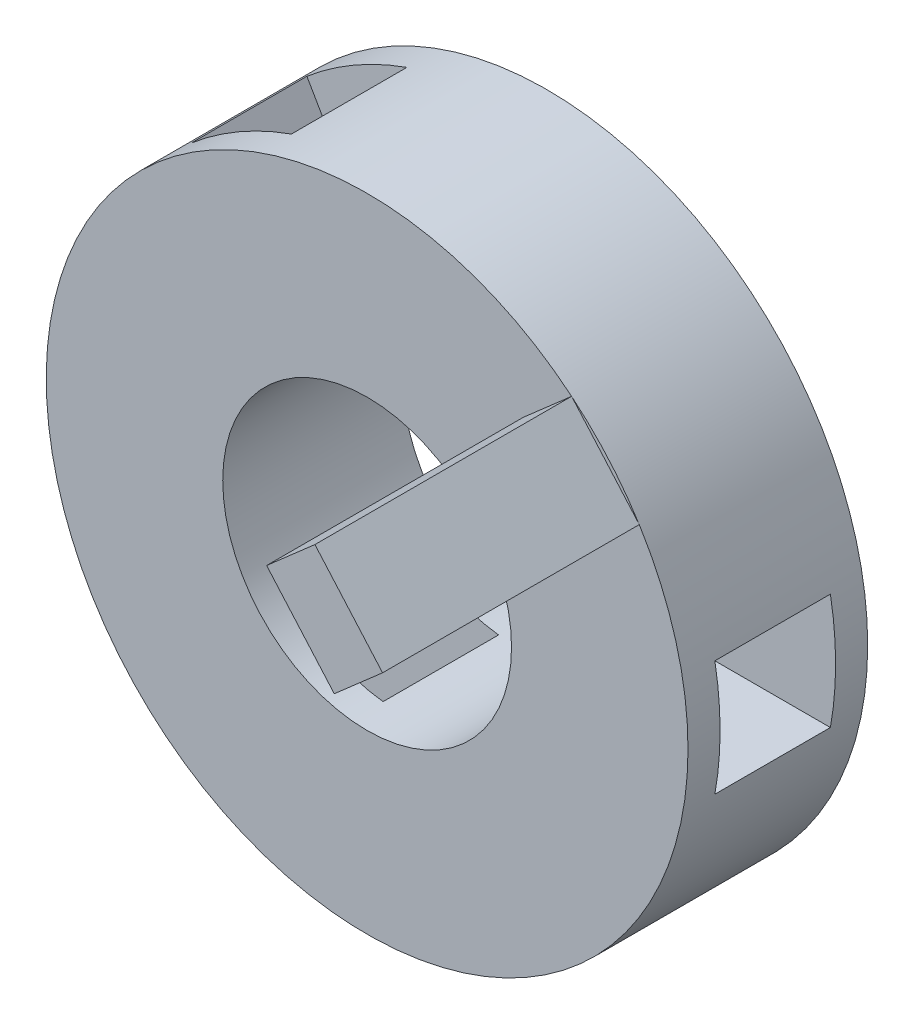
SolidWorks part; units mm, degrees
ref_plane "Plan de face" through (0, 0, 0) normal (0, 0, 1) x (1, 0, 0)
ref_plane "Plan de dessus" through (0, 0, 0) normal (0, 1, 0) x (1, 0, 0)
ref_plane "Plan de droite" through (0, 0, 0) normal (1, 0, 0) x (0, 0, -1)
sketch "Esquisse1" plane through (0, 0, 0) normal (0, 0, 1) x (1, 0, 0)
  circle A0 centre (0, 0) radius 25
  dimension "D1" = 50
extrude "Boss.-Extru.1" add sketch "Esquisse1" along normal blind 14 contours A0
sketch "Esquisse2" plane through (0, 0, 0) normal (1, 0, 0) x (0, 0, -1)
  line L0 (0, -25) -> (0, 25) construction
  line L1 (-11.5, 4.5) -> (-2.5, 4.5)
  line L2 (-11.5, 4.5) -> (-11.5, -4.5)
  line L3 (-11.5, -4.5) -> (-2.5, -4.5)
  line L4 (-2.5, 4.5) -> (-2.5, -4.5)
  dimension "D1" = 9
  dimension "D2" = 9
  dimension "D3" = 2.5
  dimension "D5" = 4.5
extrude "Enlèv. mat.-Extru.1" cut sketch "Esquisse2" against normal blind 16 from offset 26
pattern_circular "Répétition circulaire1" count 3 over 360 about axis through (0, 0, 0) along (0, 0, 1) of "Enlèv. mat.-Extru.1"
sketch "Esquisse9" plane through (0, 0, 0) normal (0, 0, -1) x (-1, 0, 0)
  circle A0 centre (0, 0) radius 11.25
  dimension "D1" = 22.5
extrude "Enlèv. mat.-Extru.2" cut sketch "Esquisse9" against normal blind 16 contours A0
sketch "Esquisse10" plane through (0, 0, 0) normal (0, 0, -1) x (-1, 0, 0)
  line L0 (-15.9324, 19.2654) -> (-21.2022, 13.2464)
  line L1 (-21.2022, 13.2464) -> (-17.4403, 9.9527)
  line L2 (-17.4403, 9.9527) -> (-12.1705, 15.9718)
  line L3 (-12.1705, 15.9718) -> (-15.9324, 19.2654)
  circle A1 centre (0, 0) radius 25 construction
  dimension "D1" = 8
  dimension "D2" = 5
extrude "Boss.-Extru.3" add sketch "Esquisse10" against normal blind 20 from surface at -14 contours L1 L2 L3 L0 starting at face at (11.25, 0, 14)
